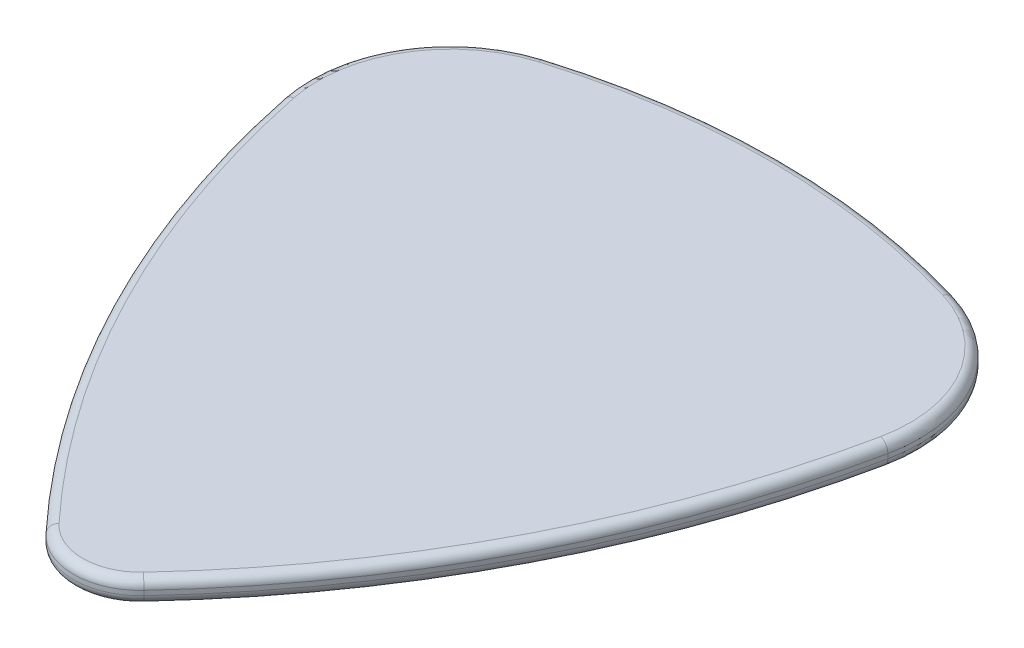
SolidWorks part; units mm, degrees
ref_plane "Front Plane" through (0, 0, 0) normal (0, 0, 1) x (1, 0, 0)
ref_plane "Top Plane" through (0, 0, 0) normal (0, 1, 0) x (1, 0, 0)
ref_plane "Right Plane" through (0, 0, 0) normal (1, 0, 0) x (0, 0, -1)
sketch "Sketch1" plane through (0, 0, 0) normal (0, 1, 0) x (1, 0, 0)
  line L0 (0, 0) -> (0, 30.62) construction
  line L1 (-13.11, 22.1848) -> (0, 22.1848) construction
  line L2 (0, 22.1848) -> (13.11, 22.1848) construction
  line L3 (0, 2.9) -> (-2.9, 2.9) construction
  line L6 (9.0762, 10.7993) -> (9.4821, 11.5846) construction
  line L7 (-7.0973, 23.4286) -> (-12.0562, 27.0493) construction
  arc A0 (-8.8774, 29.3049) -> (8.8774, 29.3049) centre (0, 0) cw
  arc A1 (-2.1219, 0.9232) -> (-13.11, 22.1848) centre (30.3499, 31.175) cw
  arc A2 (-13.11, 22.1848) -> (-8.8774, 29.3049) centre (-7.0973, 23.4286) cw
  arc A3 (2.1219, 0.9232) -> (13.11, 22.1848) centre (-30.3499, 31.175) ccw
  arc A4 (13.11, 22.1848) -> (8.8774, 29.3049) centre (7.0973, 23.4286) ccw
  arc A5 (-2.1219, 0.9232) -> (2.1219, 0.9232) centre (0, 2.9) ccw
  circle A6 centre (-7.0973, 23.4286) radius 6.14 construction
  circle A7 centre (-30.3499, 31.175) radius 44.38 construction
  circle A8 centre (0, 2.9) radius 2.9 construction
  point P8 (0, 30.62)
  dimension "D1" = 30.62
  dimension "D2" = 26.22
  dimension "D3" = 44.38
  dimension "D4" = 6.14
  dimension "D5" = 2.9
extrude "Boss-Extrude1" add sketch "Sketch1" along normal blind 1
fillet "Fillet1" radius 0.4 12 edges at (-9.0762, 0, -10.7993) (0, 0, 0) (9.0762, 0, -10.7993) (12.3752, 0, -26.566) (0, 0, -30.62) (-12.3752, 0, -26.566) (0, 1, -30.62) (12.3752, 1, -26.566) (9.0762, 1, -10.7993) (0, 1, 0) (-9.0762, 1, -10.7993) (-12.3752, 1, -26.566)
